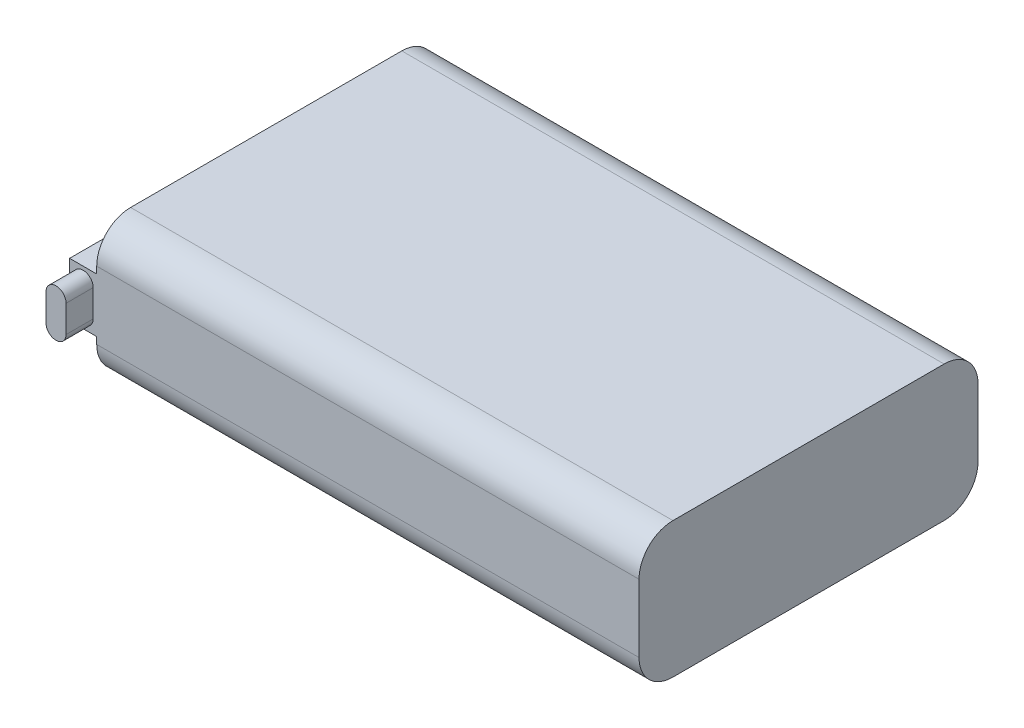
SolidWorks part; units mm, degrees
ref_plane "前视基准面" through (0, 0, 0) normal (0, 0, 1) x (1, 0, 0)
ref_plane "上视基准面" through (0, 0, 0) normal (0, 1, 0) x (1, 0, 0)
ref_plane "右视基准面" through (0, 0, 0) normal (1, 0, 0) x (0, 0, -1)
other "Configuration Table"
sketch "草图1" plane through (0, 0, 0) normal (0, 1, 0) x (1, 0, 0)
  line L1 (0, 0) -> (40, 0)
  line L2 (0, 0) -> (0, 25)
  line L3 (0, 25) -> (40, 25)
  line L4 (40, 0) -> (40, 25)
  dimension "D1" = 25
  dimension "D2" = 40
extrude "凸台-拉伸1" add sketch "草图1" along normal blind 10
fillet "圆角1" radius 2.5 4 edges at (20, 10, 0) (20, 10, -25) (20, 0, -25) (20, 0, 0)
sketch "草图2" plane through (0, 0, 0) normal (-1, 0, 0) x (0, 0, 1)
  line L0 (-25, 7.5) -> (-25, 2.5) construction
  line L1 (-25, 7) -> (0, 7)
  line L2 (-25, 7) -> (-25, 3)
  line L3 (-25, 3) -> (0, 3)
  line L4 (0, 7) -> (0, 3)
  line L5 (0, 7.5) -> (0, 2.5) construction
  line L6 (-25, 5) -> (0, 5) construction
  point P10 (0, 0)
  dimension "D1" = 4
extrude "凸台-拉伸2" add sketch "草图2" along normal blind 2
sketch "草图3" plane through (0, 0, 0) normal (0, 0, 1) x (1, 0, 0)
  line L0 (-1, 6) -> (-1, 4) construction
  line L1 (-0.26, 6) -> (-0.26, 4)
  line L2 (-1.74, 6) -> (-1.74, 4)
  line L3 (-2, 3) -> (-2, 7) construction
  line L4 (-1, 5) -> (-2, 5) construction
  arc A0 (-0.26, 6) -> (-1.74, 6) centre (-1, 6) ccw
  arc A1 (-1.74, 4) -> (-0.26, 4) centre (-1, 4) ccw
  point P2 (-1, 5)
  dimension "D3" = 0.74
  dimension "D1" = 1
  dimension "D2" = 2
extrude "凸台-拉伸3" add sketch "草图3" along normal blind 2
